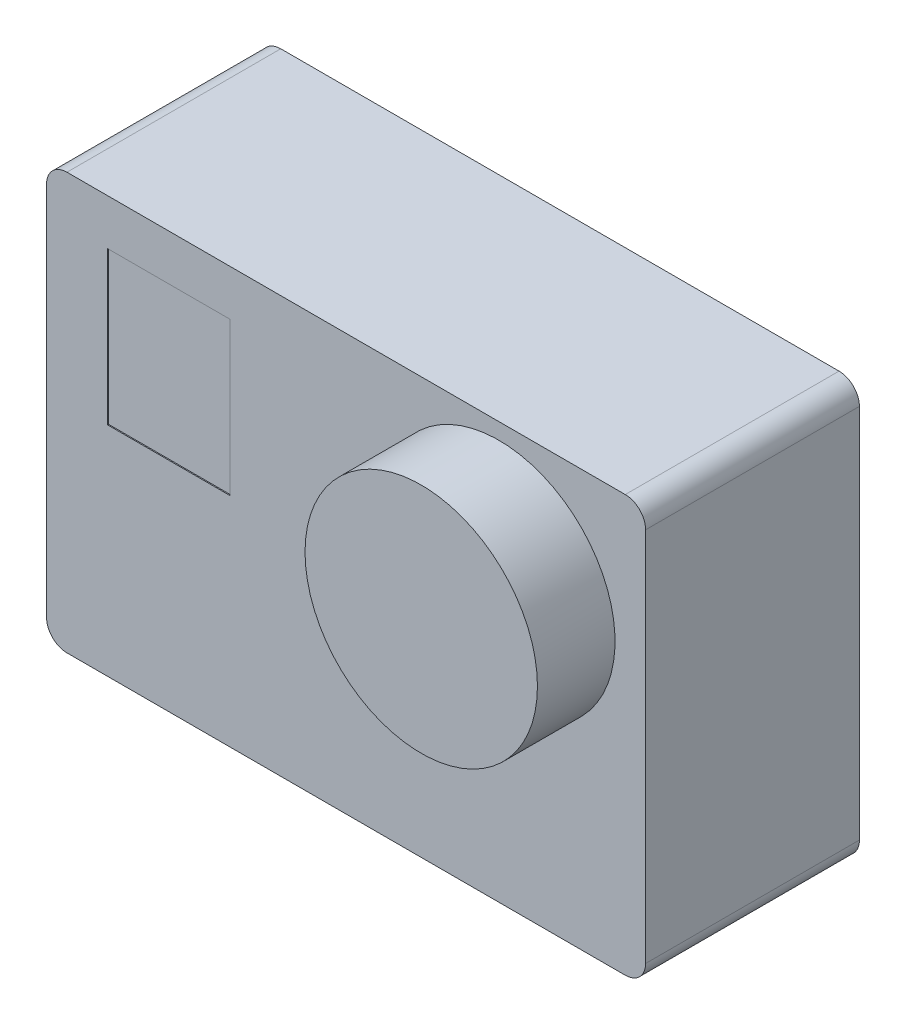
SolidWorks part; units mm, degrees
ref_plane "Front Plane" through (0, 0, 0) normal (0, 0, 1) x (1, 0, 0)
ref_plane "Top Plane" through (0, 0, 0) normal (0, 1, 0) x (1, 0, 0)
ref_plane "Right Plane" through (0, 0, 0) normal (1, 0, 0) x (0, 0, -1)
sketch "Sketch1" plane through (0, 0, 0) normal (0, 0, 1) x (1, 0, 0)
  line L1 (-29.42, -20.445) -> (29.42, -20.445)
  line L2 (-29.42, -20.445) -> (-29.42, 20.445)
  line L3 (-29.42, 20.445) -> (29.42, 20.445)
  line L4 (29.42, -20.445) -> (29.42, 20.445)
  line L5 (-29.42, -20.445) -> (29.42, 20.445) construction
  line L6 (-29.42, 20.445) -> (29.42, -20.445) construction
  point P0 (0, 0)
  dimension "D1" = 58.84
  dimension "D2" = 40.89
extrude "Boss-Extrude1" add sketch "Sketch1" along normal mid plane 21
sketch "Sketch2" plane through (0, 0, 10.5) normal (0, 0, 1) x (1, 0, 0)
  line L0 (29.42, 20.445) -> (-29.42, 20.445) construction
  circle A0 centre (15, 7.445) radius 11.415
  point P2 (15.8029, 6.5391)
  dimension "D1" = 22.83
  dimension "D2" = 15
  dimension "D3" = 13
extrude "Boss-Extrude2" add sketch "Sketch2" along normal blind 7.62
sketch "Sketch4" plane through (0, 0, 10.5) normal (0, 0, 1) x (1, 0, 0)
  line L1 (-11.42, 0.945) -> (-23.42, 0.945)
  line L2 (-11.42, 0.945) -> (-11.42, 15.945)
  line L3 (-11.42, 15.945) -> (-23.42, 15.945)
  line L4 (-23.42, 0.945) -> (-23.42, 15.945)
  line L5 (-11.42, 0.945) -> (-23.42, 15.945) construction
  line L6 (-11.42, 15.945) -> (-23.42, 0.945) construction
  line L7 (29.42, 20.445) -> (-29.42, 20.445) construction
  line L8 (-29.42, 20.445) -> (-29.42, -20.445) construction
  point P0 (-17.42, 8.445)
  point P9 (-47.9535, 16.8322)
  dimension "D1" = 12
  dimension "D2" = 15
  dimension "D3" = 12
  dimension "D4" = 12
extrude "Cut-Extrude1" cut sketch "Sketch4" against normal blind 0.1
fillet "Fillet1" radius 2 4 edges at (29.42, -20.445, 0) (-29.42, -20.445, 0) (-29.42, 20.445, 0) (29.42, 20.445, 0)
